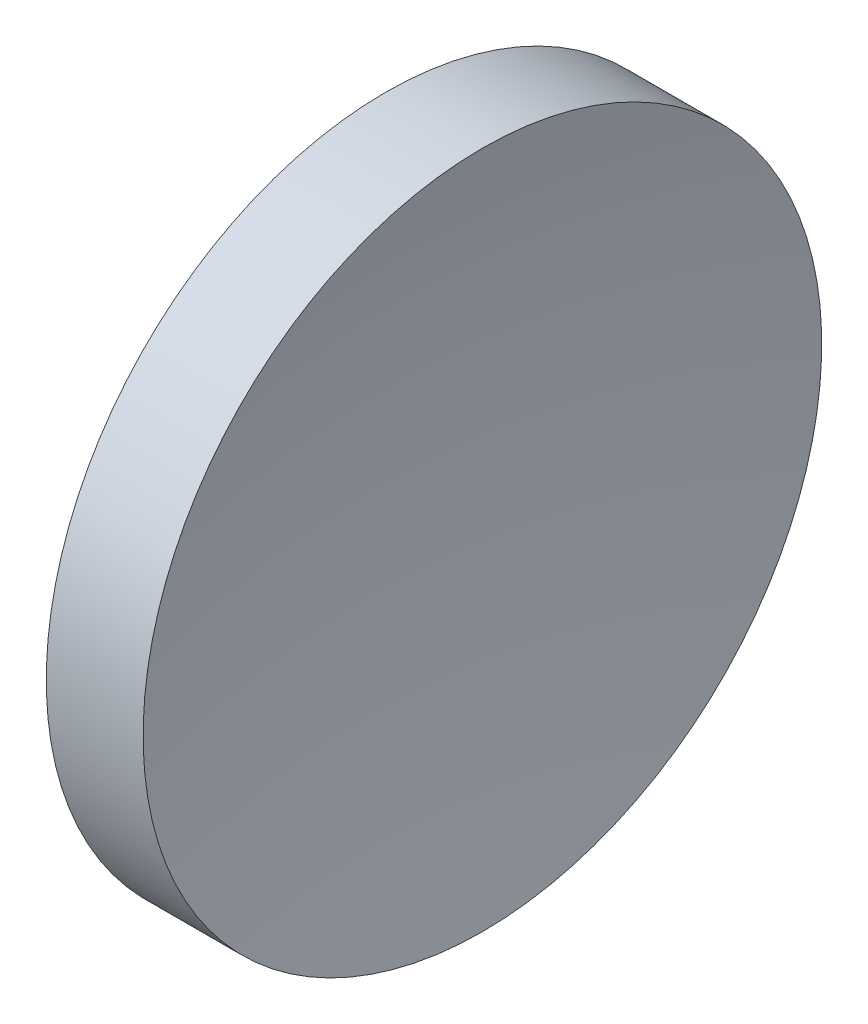
SolidWorks part; units mm, degrees
ref_plane "前视基准面" through (0, 0, 0) normal (0, 0, 1) x (1, 0, 0)
ref_plane "上视基准面" through (0, 0, 0) normal (0, 1, 0) x (1, 0, 0)
ref_plane "右视基准面" through (0, 0, 0) normal (1, 0, 0) x (0, 0, -1)
sketch "草图1" plane through (0, 0, 0) normal (0, 0, 1) x (1, 0, 0)
  line L0 (43.012, 26.0623) -> (51.5611, 26.0623) construction
  line L1 (44.8544, 26.0623) -> (44.8544, 34.0623)
  line L2 (44.8544, 34.0623) -> (47.1373, 34.0623)
  line L3 (46.3544, 26.0623) -> (44.8544, 26.0623)
  arc A0 (47.1373, 34.0623) -> (46.3544, 26.0623) centre (87.6544, 26.0587) ccw
revolve "旋转1" add sketch "草图1" angle 360 about L0
